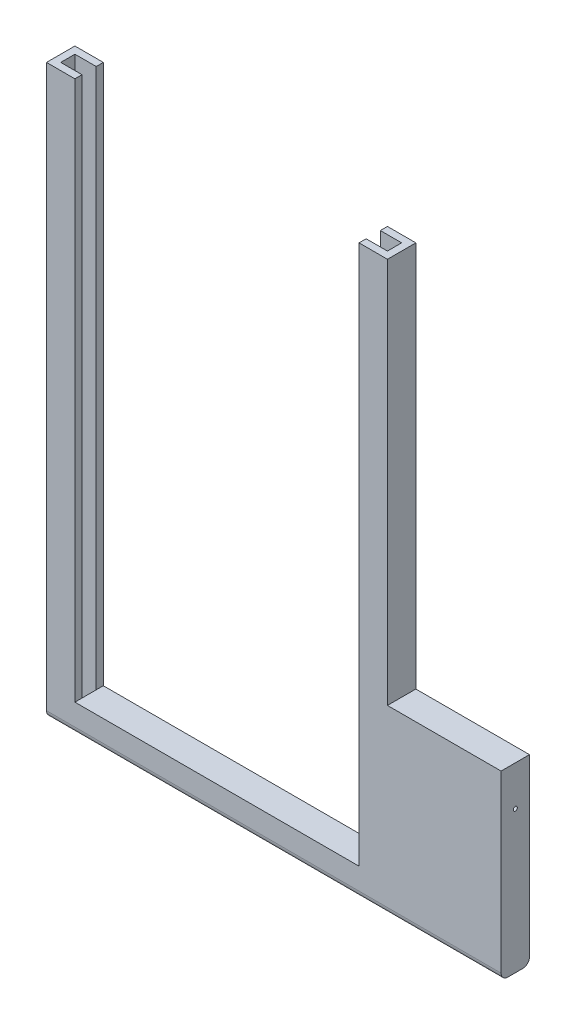
SolidWorks part; units mm, degrees
ref_plane "Front Plane" through (0, 0, 0) normal (0, 0, 1) x (1, 0, 0)
ref_plane "Top Plane" through (0, 0, 0) normal (0, 1, 0) x (1, 0, 0)
ref_plane "Right Plane" through (0, 0, 0) normal (1, 0, 0) x (0, 0, -1)
other "Center of Mass"
sketch "Sketch1" plane through (0, 0, 0) normal (0, 0, 1) x (1, 0, 0)
  line L0 (0, 0) -> (0, 100)
  line L1 (0, 100) -> (5, 100)
  line L2 (5, 100) -> (5, 5)
  line L3 (5, 5) -> (55, 5)
  line L4 (55, 5) -> (55, 100)
  line L5 (55, 100) -> (60, 100)
  line L7 (80, 0) -> (0, 0)
  line L11 (60, 50) -> (60, 100)
  line L14 (60, 50) -> (60, 32)
  line L15 (60, 32) -> (80, 32)
  line L16 (80, 32) -> (80, 0)
  dimension "D1" = 50
  dimension "D2" = 5
  dimension "D3" = 5
  dimension "D4" = 80
  dimension "D5" = 5
  dimension "D6" = 100
  dimension "D7" = 50
  dimension "D8" = 18
  dimension "D9" = 32
extrude "Boss-Extrude1" add sketch "Sketch1" along normal blind 5
sketch "Sketch4" plane through (0, 100, 0) normal (0, 1, 0) x (1, 0, 0)
  line L0 (55, -3.75) -> (55, -1.25)
  line L1 (55, -5) -> (55, 0) construction
  line L2 (55, -1.25) -> (58.75, -1.25)
  line L3 (58.75, -1.25) -> (58.75, -3.75)
  line L4 (58.75, -3.75) -> (55, -3.75)
  line L5 (5, -3.75) -> (5, -1.25)
  line L6 (5, -5) -> (5, 0) construction
  line L7 (5, -1.25) -> (1.25, -1.25)
  line L8 (1.25, -1.25) -> (1.25, -3.75)
  line L9 (1.25, -3.75) -> (5, -3.75)
  dimension "D1" = 2.5
  dimension "D2" = 3.75
  dimension "D3" = 1.25
  dimension "D4" = 2.5
  dimension "D5" = 3.75
  dimension "D6" = 1.25
extrude "Cut-Extrude2" cut sketch "Sketch4" against normal through all
sketch "Sketch5" plane through (80, 0, 0) normal (1, 0, 0) x (0, 0, -1)
  circle A0 centre (-2.5, 25) radius 0.36
extrude "Cut-Extrude3" cut sketch "Sketch5" against normal through all
fillet "Fillet1" radius 1.2 1 edges at (40, 0, 0)
fillet "Fillet2" radius 1.2 1 edges at (40, 0, 5)
